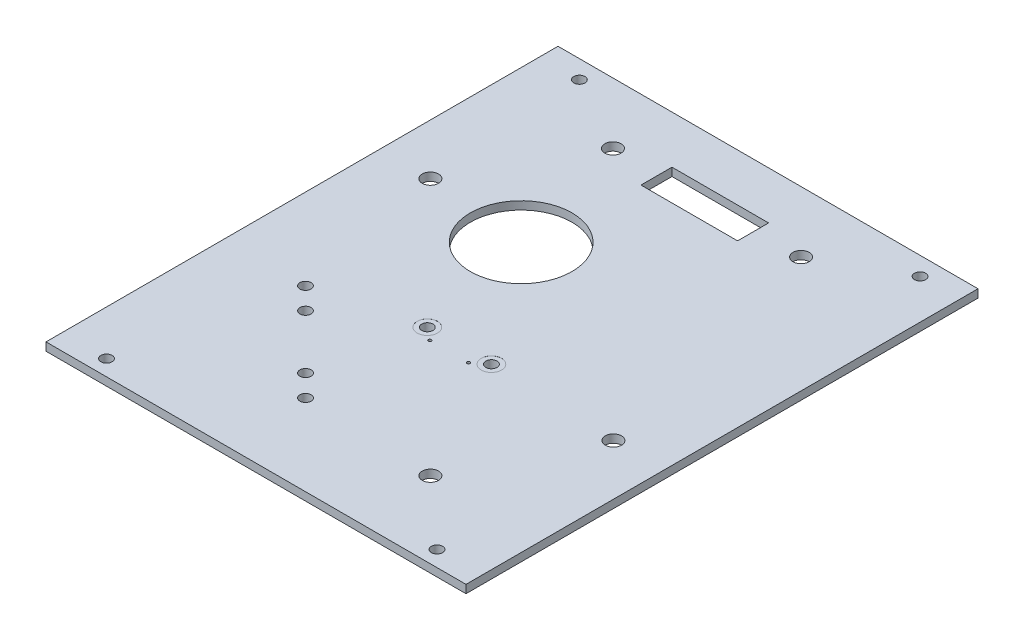
SolidWorks part; units mm, degrees
material "電力回路基板"
ref_plane "Front Plane" through (0, 0, 0) normal (0, 0, 1) x (1, 0, 0)
ref_plane "Top Plane" through (0, 0, 0) normal (0, 1, 0) x (1, 0, 0)
ref_plane "Right Plane" through (0, 0, 0) normal (1, 0, 0) x (0, 0, -1)
sketch "Sketch1" plane through (0, 0, 0) normal (0, 1, 0) x (1, 0, 0)
  line L0 (65.24, 0.2725) -> (65.24, -46.4375)
  line L1 (-17.76, 29.8625) -> (65.24, 29.8625)
  line L2 (65.24, 29.8625) -> (65.24, 21.5625)
  line L3 (-17.76, 4.3625) -> (-17.76, -45.7898)
  line L6 (65.24, -63.6375) -> (65.24, -70.1375)
  line L7 (65.24, -70.1375) -> (-17.76, -70.1375)
  line L8 (-17.76, -70.1375) -> (-17.76, -63.6375)
  line L11 (-17.76, 29.8625) -> (-17.76, 21.5625)
  line L17 (-17.76, -48.6375) -> (-17.76, -45.7898)
  line L21 (65.24, 6.5625) -> (65.24, 0.2725)
  line L22 (-17.76, 21.5625) -> (-17.76, 4.3625)
  line L23 (-17.76, -48.6375) -> (-17.76, -63.6375)
  line L24 (65.24, -46.4375) -> (65.24, -63.6375)
  line L25 (65.24, 6.5625) -> (65.24, 21.5625)
  circle A0 centre (20.04, -29.2375) radius 0.3
  circle A1 centre (27.74, -29.2375) radius 0.3
  dimension "D3" = 0.6
  dimension "D7" = 37.8
  dimension "D8" = 40.9
  dimension "D9" = 37.5
  dimension "D10" = 40.9
  dimension "D1" = 100
  dimension "D2" = 83
  dimension "D4" = 6.5
  dimension "D5" = 6.5
  dimension "D6" = 8.3
extrude "Boss-Extrude1" add sketch "Sketch1" along normal blind 1.6 contours L11 L22 L3 L17 L23 L8 L7 L6 L24 L0 L21 L25 L2 L1
hole_wizard "Ø2.2 (2.2) Diameter Hole1" positions "Sketch6" profile "Sketch5" hole size "Ø2.2" standard "ANSI Metric"
sketch "Sketch6" plane through (0, 1.6, 0) normal (0, 1, 0) x (1, 0, 0)
  line L2 (-17.76, 29.8625) -> (65.24, 29.8625) construction
  line L3 (-17.76, 29.8625) -> (-17.76, -70.1375) construction
  line L4 (65.24, 29.8625) -> (65.24, -70.1375) construction
  point P27 (57.24, 27.8625)
  point P29 (-9.76, 27.8625)
  dimension "D3" = 2
  dimension "D4" = 8
  dimension "D5" = 2
  dimension "D6" = 8
sketch "Sketch5" plane through (57.24, 1.6, -27.8625) normal (1, 0, 0) x (0, 0, 1)
  line L0 (0, 0) -> (0, 5)
  line L1 (0, 5) -> (1.1, 5)
  line L2 (1.1, 5) -> (1.1, 0)
  line L5 (1.1, 0) -> (0, 0)
  line L10 (0, 5) -> (-1.1, 5) construction
  line L11 (0, -6.35) -> (0, 107.95) construction
  dimension "Hole Dia." = 2.2
  dimension "Hole Depth" = 5
  dimension "Drill Angle" = 180
sketch "Sketch9" plane through (0, 0, 0) normal (0, -1, 0) x (-1, 0, 0)
  line L0 (-65.24, 29.8625) -> (-65.24, -70.1375) construction
  line L3 (-65.24, -70.1375) -> (17.76, -70.1375) construction
  circle A0 centre (-12.19, -5.5375) radius 10
  dimension "D1" = 53.05
  dimension "D2" = 64.6
  dimension "D4" = 20
extrude "Cut-Extrude4" cut sketch "Sketch9" against normal through all
sketch "Sketch15" plane through (0, 0, 0) normal (0, -1, 0) x (1, 0, 0)
  line L0 (-17.76, -29.8625) -> (-17.76, 70.1375) construction
  line L1 (65.24, 70.1375) -> (-17.76, 70.1375)
  line L2 (65.24, 70.1375) -> (65.24, 67.6375)
  line L3 (65.24, 67.6375) -> (-17.76, 67.6375)
  line L4 (-17.76, 70.1375) -> (-17.76, 67.6375)
  dimension "D1" = 2.5
extrude "Cut-Extrude8" cut sketch "Sketch15" against normal through all
sketch "Sketch16" plane through (0, 0, 0) normal (0, -1, 0) x (1, 0, 0)
  line L3 (-17.76, -29.8625) -> (65.24, -29.8625) construction
  line L5 (65.24, -29.8625) -> (65.24, 67.6375) construction
  line L6 (-17.76, -29.8625) -> (-17.76, 67.6375) construction
  line L7 (-17.76, 67.6375) -> (65.24, 67.6375) construction
  circle A0 centre (5.24, 56.6375) radius 1.5
  circle A1 centre (42.24, 56.6375) radius 1.5
  circle A5 centre (-13.76, 5.6375) radius 1.5
  circle A6 centre (61.24, 5.6375) radius 1.5
  circle A7 centre (2.24, 5.6375) radius 1.5
  point P2 (42.24, 56.6375)
  point P3 (5.24, 56.6375)
  point P23 (61.24, 5.6375)
  point P24 (-13.76, 5.6375)
  dimension "D10" = 3
  dimension "D11" = 3
  dimension "D19" = 3
  dimension "D20" = 3
  dimension "D21" = 3
  dimension "D22" = 20
  dimension "D23" = 62
  dimension "D5" = 11
  dimension "D6" = 23
  dimension "D7" = 11
  dimension "D8" = 23
  dimension "D15" = 35.5
  dimension "D16" = 35.5
  dimension "D17" = 4
  dimension "D18" = 4
sketch "Sketch37" plane through (0, 0, -29.8625) normal (0, 0, -1) x (-1, 0, 0)
  line L1 (17.76, 1.6) -> (-65.24, 1.6)
  line L2 (17.76, 1.6) -> (17.76, 0)
  line L3 (17.76, 0) -> (-65.24, 0)
  line L4 (-65.24, 1.6) -> (-65.24, 0)
extrude "Extrude1" add sketch "Sketch37" along normal blind 1.6
sketch "Sketch38" plane through (0, 0, 67.6375) normal (0, 0, 1) x (1, 0, 0)
  line L1 (65.24, 1.6) -> (-17.76, 1.6)
  line L2 (65.24, 1.6) -> (65.24, 0)
  line L3 (65.24, 0) -> (-17.76, 0)
  line L4 (-17.76, 1.6) -> (-17.76, 0)
extrude "Extrude2" add sketch "Sketch38" along normal blind 1.6
sketch "Sketch39" plane through (0, 1.6, 0) normal (0, 1, 0) x (1, 0, 0)
  line L0 (-17.76, -69.2375) -> (-17.76, 31.4625) construction
  line L1 (65.24, 31.4625) -> (65.24, -69.2375) construction
  line L2 (65.24, -69.2375) -> (-17.76, -69.2375) construction
  point P0 (-8.76, -66.1375)
  point P1 (56.24, -66.1375)
  dimension "D1" = 9
  dimension "D2" = 9
  dimension "D3" = 3.1
  dimension "D4" = 3.1
hole_wizard "Ø2.2 (2.2) Diameter Hole4" positions "Sketch41" profile "Sketch40" hole size "Ø2.2" standard "ANSI Metric"
sketch "Sketch41" plane through (0, 1.6, 0) normal (0, 1, 0) x (1, 0, 0)
  point P0 (-8.76, -66.1375)
  point P3 (56.24, -66.1375)
sketch "Sketch40" plane through (-8.76, 1.6, 66.1375) normal (1, 0, 0) x (0, 0, 1)
  line L0 (0, 0) -> (0, 1.6)
  line L1 (0, 1.6) -> (1.1, 1.6)
  line L2 (1.1, 1.6) -> (1.1, 0)
  line L5 (1.1, 0) -> (0, 0)
  line L10 (0, 1.6) -> (-1.1, 1.6) construction
  line L11 (0, -6.35) -> (0, 107.95) construction
  dimension "穴の直径" = 2.2
  dimension "穴の深さ" = 1.6
  dimension "ﾄﾞﾘﾙ角度" = 180
sketch "Sketch44" plane through (0, 0, 0) normal (0, -1, 0) x (1, 0, 0)
  line L0 (-17.76, 69.2375) -> (65.24, 69.2375) construction
  line L1 (65.24, -31.4625) -> (65.24, 69.2375) construction
  line L2 (-17.76, -31.4625) -> (-17.76, 69.2375) construction
  point P0 (43.24, 39.2375)
  point P1 (43.24, 22.2375)
  point P2 (4.24, 22.2375)
  point P3 (4.24, 39.2375)
  dimension "D1" = 30
  dimension "D2" = 22
  dimension "D3" = 22
  dimension "D4" = 17
  dimension "D5" = 17
  dimension "D6" = 30
  dimension "D7" = 22
  dimension "D8" = 22
sketch "Sketch49" plane through (0, 0, 0) normal (0, -1, 0) x (1, 0, 0)
  line L0 (-17.76, 69.2375) -> (65.24, 69.2375) construction
  line L1 (65.24, -31.4625) -> (65.04, -31.4625)
  line L2 (65.24, -31.4625) -> (65.24, 69.2375)
  line L3 (65.24, 69.2375) -> (65.04, 69.2375)
  line L4 (65.04, -31.4625) -> (65.04, 69.2375)
  line L5 (65.24, -31.4625) -> (-17.76, -31.4625) construction
  line L6 (-17.76, 69.2375) -> (-17.56, 69.2375)
  line L7 (-17.76, 69.2375) -> (-17.76, -31.4625)
  line L8 (-17.76, -31.4625) -> (-17.56, -31.4625)
  line L9 (-17.56, 69.2375) -> (-17.56, -31.4625)
  dimension "D1" = 0.2
  dimension "D2" = 0.2
extrude "Extrude5" cut sketch "Sketch49" against normal through all
sketch "Sketch52" plane through (0, 0, 0) normal (0, -1, 0) x (1, 0, 0)
  line L0 (65.04, -31.4625) -> (-17.56, -31.4625) construction
  line L1 (33.24, -15.9775) -> (14.24, -15.9775)
  line L2 (33.24, -15.9775) -> (33.24, -22.0775)
  line L3 (33.24, -22.0775) -> (14.24, -22.0775)
  line L4 (14.24, -15.9775) -> (14.24, -22.0775)
  line L5 (33.24, -15.9775) -> (14.24, -22.0775) construction
  line L6 (33.24, -22.0775) -> (14.24, -15.9775) construction
  point P0 (23.74, -19.0275)
  point P5 (23.74, -31.4625)
  dimension "D1" = 0
  dimension "D2" = 12.435
extrude "Cut-Extrude10" cut sketch "Sketch52" against normal through all
sketch "ｽｹｯﾁ2" plane through (0, 0, 0) normal (0, -1, 0) x (-1, 0, 0)
  line L0 (17.56, -69.2375) -> (-65.04, -69.2375) construction
  line L1 (-65.04, -69.2375) -> (-65.04, 31.4625) construction
  line L3 (-65.04, 31.4625) -> (17.56, 31.4625) construction
  circle A0 centre (-55.04, -30.2375) radius 1.6
  circle A1 centre (7.56, -3.6375) radius 1.6
  circle A2 centre (-42.24, 19.4625) radius 1.6
  circle A3 centre (-5.24, 19.4625) radius 1.6
  circle A4 centre (-43.04, -54.2375) radius 1.6
  dimension "D1" = 39
  dimension "D2" = 10
  dimension "D3" = 72.6
  dimension "D4" = 65.6
  dimension "D5" = 59.8
  dimension "D6" = 22.8
  dimension "D7" = 88.7
  dimension "D9" = 15
  dimension "D10" = 22
  dimension "D8" = 12
extrude "ｶｯﾄ - 押し出し2" cut sketch "ｽｹｯﾁ2" against normal blind 10
sketch "ｽｹｯﾁ8" plane through (0, 1.6, 0) normal (0, 1, 0) x (1, 0, 0)
  line L0 (65.04, -69.2375) -> (-17.56, -69.2375) construction
  circle A0 centre (27.54, -31.2375) radius 0.3
  circle A1 centre (19.94, -31.2375) radius 0.3
  dimension "D1" = 38
  dimension "D2" = 38
extrude "ｶｯﾄ - 押し出し3" cut sketch "ｽｹｯﾁ8" against normal blind 10
sketch "ｽｹｯﾁ9" plane through (0, 1.6, 0) normal (0, 1, 0) x (1, 0, 0)
  line L0 (65.04, -69.2375) -> (-17.56, -69.2375) construction
  line L1 (-17.56, 31.4625) -> (-17.56, -69.2375) construction
  line L2 (65.04, -69.2375) -> (65.04, 31.4625) construction
  circle A0 centre (30.04, -29.2375) radius 1.1
  circle A1 centre (17.44, -29.2375) radius 1.1
  dimension "D1" = 40
  dimension "D2" = 40
  dimension "D3" = 35
  dimension "D4" = 35
extrude "ｶｯﾄ - 押し出し4" cut sketch "ｽｹｯﾁ9" against normal blind 10
sketch "ｽｹｯﾁ10" plane through (0, 1.6, 0) normal (0, 1, 0) x (1, 0, 0)
  circle A0 centre (30.04, -29.2375) radius 2
  circle A1 centre (17.44, -29.2375) radius 2
extrude "ｶｯﾄ - 押し出し5" cut sketch "ｽｹｯﾁ10" against normal blind 0.01
sketch "ｽｹｯﾁ11" plane through (0, 0, 0) normal (0, -1, 0) x (1, 0, 0)
  line L0 (-17.56, 69.2375) -> (65.04, 69.2375) construction
  line L1 (65.04, 69.2375) -> (65.04, -31.4625) construction
  circle A0 centre (17.5126, 53.2701) radius 1.1
  circle A1 centre (13.27, 49.0275) radius 1.1
  circle A2 centre (2.66, 38.4175) radius 1.1
  circle A3 centre (-1.5876, 34.1798) radius 1.1
  dimension "D1" = 6
  dimension "D2" = 6
  dimension "D3" = 51.77
  dimension "D4" = 20.21
  dimension "D5" = 30.82
  dimension "D6" = 62.38
extrude "ｶｯﾄ - 押し出し6" cut sketch "ｽｹｯﾁ11" against normal blind 10
